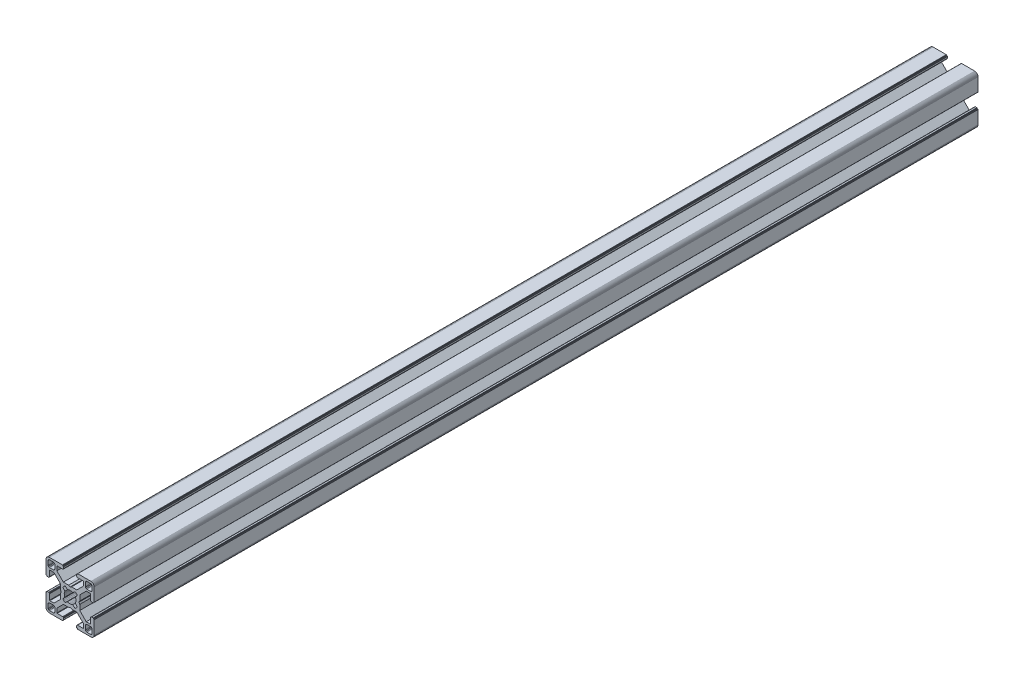
SolidWorks part; units mm, degrees
ref_plane "Front Plane" through (0, 0, 0) normal (0, 0, 1) x (1, 0, 0)
ref_plane "Top Plane" through (0, 0, 0) normal (0, 1, 0) x (1, 0, 0)
ref_plane "Right Plane" through (0, 0, 0) normal (1, 0, 0) x (0, 0, -1)
ref_plane "Plane1" through (0, 0, 0) normal (0, 0, 1) x (1, 0, 0)
sketch "Sketch1" plane through (0, 0, 0) normal (0, 0, 1) x (1, 0, 0)
  line L0 (28.3473, 29.9696) -> (28, 30)
  line L1 (28, 30) -> (19.75, 30)
  line L2 (19.75, 30) -> (19.7153, 29.997)
  line L3 (19.7153, 29.997) -> (19.6816, 29.9879)
  line L4 (19.6816, 29.9879) -> (19.65, 29.9732)
  line L5 (19.65, 29.9732) -> (19.6214, 29.9532)
  line L6 (19.6214, 29.9532) -> (19.5968, 29.9286)
  line L7 (19.5968, 29.9286) -> (19.5768, 29.9)
  line L8 (19.5768, 29.9) -> (19.5621, 29.8684)
  line L9 (19.5621, 29.8684) -> (19.553, 29.8347)
  line L10 (19.553, 29.8347) -> (19.55, 29.8)
  line L11 (19.55, 29.8) -> (19.55, 29.7)
  line L12 (19.55, 29.7) -> (19.547, 29.6653)
  line L13 (19.547, 29.6653) -> (19.5379, 29.6316)
  line L14 (19.5379, 29.6316) -> (19.5232, 29.6)
  line L15 (19.5232, 29.6) -> (19.5032, 29.5714)
  line L16 (19.5032, 29.5714) -> (19.4786, 29.5468)
  line L17 (19.4786, 29.5468) -> (19.45, 29.5268)
  line L18 (19.45, 29.5268) -> (19.4184, 29.5121)
  line L19 (19.4184, 29.5121) -> (19.3847, 29.503)
  line L20 (19.3847, 29.503) -> (19.35, 29.5)
  line L21 (19.35, 29.5) -> (19.25, 29.5)
  line L22 (19.25, 29.5) -> (19.2153, 29.497)
  line L23 (19.2153, 29.497) -> (19.1816, 29.4879)
  line L24 (19.1816, 29.4879) -> (19.15, 29.4732)
  line L25 (19.15, 29.4732) -> (19.1214, 29.4532)
  line L26 (19.1214, 29.4532) -> (19.0968, 29.4286)
  line L27 (19.0968, 29.4286) -> (19.0768, 29.4)
  line L28 (19.0768, 29.4) -> (19.0621, 29.3684)
  line L29 (19.0621, 29.3684) -> (19.053, 29.3347)
  line L30 (19.053, 29.3347) -> (19.05, 29.3)
  line L31 (19.05, 29.3) -> (19.05, 28.4)
  line L32 (19.05, 28.4) -> (19.0591, 28.2958)
  line L33 (19.0591, 28.2958) -> (19.0862, 28.1948)
  line L34 (19.0862, 28.1948) -> (19.1304, 28.1)
  line L35 (19.1304, 28.1) -> (19.1904, 28.0143)
  line L36 (19.1904, 28.0143) -> (19.2643, 27.9404)
  line L37 (19.2643, 27.9404) -> (19.35, 27.8804)
  line L38 (19.35, 27.8804) -> (19.4448, 27.8362)
  line L39 (19.4448, 27.8362) -> (19.5458, 27.8091)
  line L40 (19.5458, 27.8091) -> (19.65, 27.8)
  line L41 (19.65, 27.8) -> (23.05, 27.8)
  line L42 (23.05, 27.8) -> (23.0847, 27.7969)
  line L43 (23.0847, 27.7969) -> (23.1184, 27.7879)
  line L44 (23.1184, 27.7879) -> (23.15, 27.7732)
  line L45 (23.15, 27.7732) -> (23.1786, 27.7532)
  line L46 (23.1786, 27.7532) -> (23.2032, 27.7285)
  line L47 (23.2032, 27.7285) -> (23.2232, 27.7)
  line L48 (23.2232, 27.7) -> (23.2379, 27.6684)
  line L49 (23.2379, 27.6684) -> (23.247, 27.6347)
  line L50 (23.247, 27.6347) -> (23.25, 27.6)
  line L51 (23.25, 27.6) -> (23.25, 25.05)
  line L52 (23.25, 25.05) -> (19.2045, 21)
  line L53 (19.2045, 21) -> (15.9, 21)
  line L54 (15.9, 21) -> (15, 20.4848)
  line L55 (15, 20.4848) -> (14.1, 21)
  line L56 (14.1, 21) -> (10.7955, 21)
  line L57 (10.7955, 21) -> (7.9973, 23.8013)
  line L58 (7.9973, 23.8013) -> (6.75, 25.05)
  line L59 (6.75, 25.05) -> (6.75, 27.6)
  line L60 (6.75, 27.6) -> (6.753, 27.6347)
  line L61 (6.753, 27.6347) -> (6.7621, 27.6684)
  line L62 (6.7621, 27.6684) -> (6.7768, 27.7)
  line L63 (6.7768, 27.7) -> (6.7968, 27.7285)
  line L64 (6.7968, 27.7285) -> (6.8215, 27.7532)
  line L65 (6.8215, 27.7532) -> (6.85, 27.7732)
  line L66 (6.85, 27.7732) -> (6.8816, 27.7879)
  line L67 (6.8816, 27.7879) -> (6.9153, 27.7969)
  line L68 (6.9153, 27.7969) -> (6.95, 27.8)
  line L69 (6.95, 27.8) -> (10.35, 27.8)
  line L70 (10.35, 27.8) -> (10.4542, 27.8091)
  line L71 (10.4542, 27.8091) -> (10.5552, 27.8362)
  line L72 (10.5552, 27.8362) -> (10.65, 27.8804)
  line L73 (10.65, 27.8804) -> (10.7357, 27.9404)
  line L74 (10.7357, 27.9404) -> (10.8096, 28.0143)
  line L75 (10.8096, 28.0143) -> (10.8696, 28.1)
  line L76 (10.8696, 28.1) -> (10.9138, 28.1948)
  line L77 (10.9138, 28.1948) -> (10.9409, 28.2958)
  line L78 (10.9409, 28.2958) -> (10.95, 28.4)
  line L79 (10.95, 28.4) -> (10.95, 29.3)
  line L80 (10.95, 29.3) -> (10.947, 29.3347)
  line L81 (10.947, 29.3347) -> (10.938, 29.3684)
  line L82 (10.938, 29.3684) -> (10.9232, 29.4)
  line L83 (10.9232, 29.4) -> (10.9032, 29.4286)
  line L84 (10.9032, 29.4286) -> (10.8786, 29.4532)
  line L85 (10.8786, 29.4532) -> (10.85, 29.4732)
  line L86 (10.85, 29.4732) -> (10.8184, 29.4879)
  line L87 (10.8184, 29.4879) -> (10.7847, 29.497)
  line L88 (10.7847, 29.497) -> (10.75, 29.5)
  line L89 (10.75, 29.5) -> (10.65, 29.5)
  line L90 (10.65, 29.5) -> (10.6153, 29.503)
  line L91 (10.6153, 29.503) -> (10.5816, 29.5121)
  line L92 (10.5816, 29.5121) -> (10.55, 29.5268)
  line L93 (10.55, 29.5268) -> (10.5214, 29.5468)
  line L94 (10.5214, 29.5468) -> (10.4968, 29.5714)
  line L95 (10.4968, 29.5714) -> (10.4768, 29.6)
  line L96 (10.4768, 29.6) -> (10.4621, 29.6316)
  line L97 (10.4621, 29.6316) -> (10.453, 29.6653)
  line L98 (10.453, 29.6653) -> (10.45, 29.7)
  line L99 (10.45, 29.7) -> (10.45, 29.8)
  line L100 (10.45, 29.8) -> (10.447, 29.8347)
  line L101 (10.447, 29.8347) -> (10.4379, 29.8684)
  line L102 (10.4379, 29.8684) -> (10.4232, 29.9)
  line L103 (10.4232, 29.9) -> (10.4032, 29.9286)
  line L104 (10.4032, 29.9286) -> (10.3786, 29.9532)
  line L105 (10.3786, 29.9532) -> (10.35, 29.9732)
  line L106 (10.35, 29.9732) -> (10.3184, 29.9879)
  line L107 (10.3184, 29.9879) -> (10.2847, 29.997)
  line L108 (10.2847, 29.997) -> (10.25, 30)
  line L109 (10.25, 30) -> (2, 30)
  line L110 (2, 30) -> (1.6527, 29.9696)
  line L111 (1.6527, 29.9696) -> (1.316, 29.8794)
  line L112 (1.316, 29.8794) -> (1, 29.7321)
  line L113 (1, 29.7321) -> (0.7144, 29.5321)
  line L114 (0.7144, 29.5321) -> (0.4679, 29.2856)
  line L115 (0.4679, 29.2856) -> (0.2679, 29)
  line L116 (0.2679, 29) -> (0.1206, 28.684)
  line L117 (0.1206, 28.684) -> (0.0304, 28.3473)
  line L118 (0.0304, 28.3473) -> (0, 28)
  line L119 (0, 28) -> (0, 19.75)
  line L120 (0, 19.75) -> (0.003, 19.7153)
  line L121 (0.003, 19.7153) -> (0.0121, 19.6816)
  line L122 (0.0121, 19.6816) -> (0.0268, 19.65)
  line L123 (0.0268, 19.65) -> (0.0468, 19.6214)
  line L124 (0.0468, 19.6214) -> (0.0714, 19.5968)
  line L125 (0.0714, 19.5968) -> (0.1, 19.5768)
  line L126 (0.1, 19.5768) -> (0.1316, 19.5621)
  line L127 (0.1316, 19.5621) -> (0.1653, 19.553)
  line L128 (0.1653, 19.553) -> (0.2, 19.55)
  line L129 (0.2, 19.55) -> (0.3, 19.55)
  line L130 (0.3, 19.55) -> (0.3347, 19.547)
  line L131 (0.3347, 19.547) -> (0.3684, 19.5379)
  line L132 (0.3684, 19.5379) -> (0.4, 19.5232)
  line L133 (0.4, 19.5232) -> (0.4286, 19.5032)
  line L134 (0.4286, 19.5032) -> (0.4532, 19.4786)
  line L135 (0.4532, 19.4786) -> (0.4732, 19.45)
  line L136 (0.4732, 19.45) -> (0.4879, 19.4184)
  line L137 (0.4879, 19.4184) -> (0.497, 19.3847)
  line L138 (0.497, 19.3847) -> (0.5, 19.35)
  line L139 (0.5, 19.35) -> (0.5, 19.25)
  line L140 (0.5, 19.25) -> (0.503, 19.2153)
  line L141 (0.503, 19.2153) -> (0.5121, 19.1816)
  line L142 (0.5121, 19.1816) -> (0.5268, 19.15)
  line L143 (0.5268, 19.15) -> (0.5468, 19.1214)
  line L144 (0.5468, 19.1214) -> (0.5714, 19.0968)
  line L145 (0.5714, 19.0968) -> (0.6, 19.0768)
  line L146 (0.6, 19.0768) -> (0.6316, 19.0621)
  line L147 (0.6316, 19.0621) -> (0.6653, 19.053)
  line L148 (0.6653, 19.053) -> (0.7, 19.05)
  line L149 (0.7, 19.05) -> (1.6, 19.05)
  line L150 (1.6, 19.05) -> (1.7042, 19.0591)
  line L151 (1.7042, 19.0591) -> (1.8052, 19.0862)
  line L152 (1.8052, 19.0862) -> (1.9, 19.1304)
  line L153 (1.9, 19.1304) -> (1.9857, 19.1904)
  line L154 (1.9857, 19.1904) -> (2.0596, 19.2643)
  line L155 (2.0596, 19.2643) -> (2.1196, 19.35)
  line L156 (2.1196, 19.35) -> (2.1638, 19.4448)
  line L157 (2.1638, 19.4448) -> (2.1909, 19.5458)
  line L158 (2.1909, 19.5458) -> (2.2, 19.65)
  line L159 (2.2, 19.65) -> (2.2, 23.05)
  line L160 (2.2, 23.05) -> (2.203, 23.0847)
  line L161 (2.203, 23.0847) -> (2.2121, 23.1184)
  line L162 (2.2121, 23.1184) -> (2.2268, 23.15)
  line L163 (2.2268, 23.15) -> (2.2468, 23.1786)
  line L164 (2.2468, 23.1786) -> (2.2714, 23.2032)
  line L165 (2.2714, 23.2032) -> (2.3, 23.2232)
  line L166 (2.3, 23.2232) -> (2.3316, 23.2379)
  line L167 (2.3316, 23.2379) -> (2.3653, 23.247)
  line L168 (2.3653, 23.247) -> (2.4, 23.25)
  line L169 (2.4, 23.25) -> (4.95, 23.25)
  line L170 (4.95, 23.25) -> (7.9973, 20.2027)
  line L171 (7.9973, 20.2027) -> (8.9955, 19.2045)
  line L172 (8.9955, 19.2045) -> (8.9955, 15.9)
  line L173 (8.9955, 15.9) -> (9.5151, 15)
  line L174 (9.5151, 15) -> (8.9955, 14.1)
  line L175 (8.9955, 14.1) -> (8.9955, 10.7955)
  line L176 (8.9955, 10.7955) -> (4.95, 6.75)
  line L177 (4.95, 6.75) -> (2.4, 6.75)
  line L178 (2.4, 6.75) -> (2.3653, 6.753)
  line L179 (2.3653, 6.753) -> (2.3316, 6.7621)
  line L180 (2.3316, 6.7621) -> (2.3, 6.7768)
  line L181 (2.3, 6.7768) -> (2.2714, 6.7968)
  line L182 (2.2714, 6.7968) -> (2.2468, 6.8214)
  line L183 (2.2468, 6.8214) -> (2.2268, 6.85)
  line L184 (2.2268, 6.85) -> (2.2121, 6.8816)
  line L185 (2.2121, 6.8816) -> (2.203, 6.9153)
  line L186 (2.203, 6.9153) -> (2.2, 6.95)
  line L187 (2.2, 6.95) -> (2.2, 10.35)
  line L188 (2.2, 10.35) -> (2.1909, 10.4542)
  line L189 (2.1909, 10.4542) -> (2.1638, 10.5552)
  line L190 (2.1638, 10.5552) -> (2.1196, 10.65)
  line L191 (2.1196, 10.65) -> (2.0596, 10.7357)
  line L192 (2.0596, 10.7357) -> (1.9857, 10.8096)
  line L193 (1.9857, 10.8096) -> (1.9, 10.8696)
  line L194 (1.9, 10.8696) -> (1.8052, 10.9138)
  line L195 (1.8052, 10.9138) -> (1.7042, 10.9409)
  line L196 (1.7042, 10.9409) -> (1.6, 10.95)
  line L197 (1.6, 10.95) -> (0.7, 10.95)
  line L198 (0.7, 10.95) -> (0.6653, 10.9469)
  line L199 (0.6653, 10.9469) -> (0.6316, 10.9379)
  line L200 (0.6316, 10.9379) -> (0.6, 10.9232)
  line L201 (0.6, 10.9232) -> (0.5715, 10.9032)
  line L202 (0.5715, 10.9032) -> (0.5468, 10.8785)
  line L203 (0.5468, 10.8785) -> (0.5268, 10.85)
  line L204 (0.5268, 10.85) -> (0.5121, 10.8184)
  line L205 (0.5121, 10.8184) -> (0.503, 10.7847)
  line L206 (0.503, 10.7847) -> (0.5, 10.75)
  line L207 (0.5, 10.75) -> (0.5, 10.65)
  line L208 (0.5, 10.65) -> (0.497, 10.6153)
  line L209 (0.497, 10.6153) -> (0.4879, 10.5816)
  line L210 (0.4879, 10.5816) -> (0.4732, 10.55)
  line L211 (0.4732, 10.55) -> (0.4532, 10.5214)
  line L212 (0.4532, 10.5214) -> (0.4286, 10.4968)
  line L213 (0.4286, 10.4968) -> (0.4, 10.4768)
  line L214 (0.4, 10.4768) -> (0.3684, 10.4621)
  line L215 (0.3684, 10.4621) -> (0.3347, 10.453)
  line L216 (0.3347, 10.453) -> (0.3, 10.45)
  line L217 (0.3, 10.45) -> (0.2, 10.45)
  line L218 (0.2, 10.45) -> (0.1653, 10.447)
  line L219 (0.1653, 10.447) -> (0.1316, 10.4379)
  line L220 (0.1316, 10.4379) -> (0.1, 10.4232)
  line L221 (0.1, 10.4232) -> (0.0714, 10.4032)
  line L222 (0.0714, 10.4032) -> (0.0468, 10.3786)
  line L223 (0.0468, 10.3786) -> (0.0268, 10.35)
  line L224 (0.0268, 10.35) -> (0.0121, 10.3184)
  line L225 (0.0121, 10.3184) -> (0.003, 10.2847)
  line L226 (0.003, 10.2847) -> (0, 10.25)
  line L227 (0, 10.25) -> (0, 2)
  line L228 (0, 2) -> (0.0304, 1.6527)
  line L229 (0.0304, 1.6527) -> (0.1206, 1.316)
  line L230 (0.1206, 1.316) -> (0.2679, 1)
  line L231 (0.2679, 1) -> (0.4679, 0.7144)
  line L232 (0.4679, 0.7144) -> (0.7144, 0.4679)
  line L233 (0.7144, 0.4679) -> (1, 0.2679)
  line L234 (1, 0.2679) -> (1.316, 0.1206)
  line L235 (1.316, 0.1206) -> (1.6527, 0.0304)
  line L236 (1.6527, 0.0304) -> (2, 0)
  line L237 (2, 0) -> (10.25, 0)
  line L238 (10.25, 0) -> (10.2847, 0.003)
  line L239 (10.2847, 0.003) -> (10.3184, 0.0121)
  line L240 (10.3184, 0.0121) -> (10.35, 0.0268)
  line L241 (10.35, 0.0268) -> (10.3786, 0.0468)
  line L242 (10.3786, 0.0468) -> (10.4032, 0.0714)
  line L243 (10.4032, 0.0714) -> (10.4232, 0.1)
  line L244 (10.4232, 0.1) -> (10.4379, 0.1316)
  line L245 (10.4379, 0.1316) -> (10.447, 0.1653)
  line L246 (10.447, 0.1653) -> (10.45, 0.2)
  line L247 (10.45, 0.2) -> (10.45, 0.3)
  line L248 (10.45, 0.3) -> (10.453, 0.3347)
  line L249 (10.453, 0.3347) -> (10.4621, 0.3684)
  line L250 (10.4621, 0.3684) -> (10.4768, 0.4)
  line L251 (10.4768, 0.4) -> (10.4968, 0.4286)
  line L252 (10.4968, 0.4286) -> (10.5214, 0.4532)
  line L253 (10.5214, 0.4532) -> (10.55, 0.4732)
  line L254 (10.55, 0.4732) -> (10.5816, 0.4879)
  line L255 (10.5816, 0.4879) -> (10.6153, 0.497)
  line L256 (10.6153, 0.497) -> (10.65, 0.5)
  line L257 (10.65, 0.5) -> (10.75, 0.5)
  line L258 (10.75, 0.5) -> (10.7847, 0.503)
  line L259 (10.7847, 0.503) -> (10.8184, 0.5121)
  line L260 (10.8184, 0.5121) -> (10.85, 0.5268)
  line L261 (10.85, 0.5268) -> (10.8785, 0.5468)
  line L262 (10.8785, 0.5468) -> (10.9032, 0.5715)
  line L263 (10.9032, 0.5715) -> (10.9232, 0.6)
  line L264 (10.9232, 0.6) -> (10.9379, 0.6316)
  line L265 (10.9379, 0.6316) -> (10.9469, 0.6653)
  line L266 (10.9469, 0.6653) -> (10.95, 0.7)
  line L267 (10.95, 0.7) -> (10.95, 1.6)
  line L268 (10.95, 1.6) -> (10.9409, 1.7042)
  line L269 (10.9409, 1.7042) -> (10.9138, 1.8052)
  line L270 (10.9138, 1.8052) -> (10.8696, 1.9)
  line L271 (10.8696, 1.9) -> (10.8096, 1.9857)
  line L272 (10.8096, 1.9857) -> (10.7357, 2.0596)
  line L273 (10.7357, 2.0596) -> (10.65, 2.1196)
  line L274 (10.65, 2.1196) -> (10.5552, 2.1638)
  line L275 (10.5552, 2.1638) -> (10.4542, 2.1909)
  line L276 (10.4542, 2.1909) -> (10.35, 2.2)
  line L277 (10.35, 2.2) -> (6.95, 2.2)
  line L278 (6.95, 2.2) -> (6.9153, 2.203)
  line L279 (6.9153, 2.203) -> (6.8816, 2.212)
  line L280 (6.8816, 2.212) -> (6.85, 2.2268)
  line L281 (6.85, 2.2268) -> (6.8215, 2.2468)
  line L282 (6.8215, 2.2468) -> (6.7968, 2.2714)
  line L283 (6.7968, 2.2714) -> (6.7768, 2.3)
  line L284 (6.7768, 2.3) -> (6.7621, 2.3316)
  line L285 (6.7621, 2.3316) -> (6.753, 2.3653)
  line L286 (6.753, 2.3653) -> (6.75, 2.4)
  line L287 (6.75, 2.4) -> (6.75, 4.95)
  line L288 (6.75, 4.95) -> (9.7875, 7.9908)
  line L289 (9.7875, 7.9908) -> (10.7955, 9)
  line L290 (10.7955, 9) -> (14.1, 9)
  line L291 (14.1, 9) -> (15, 9.5151)
  line L292 (15, 9.5151) -> (15.9, 9)
  line L293 (15.9, 9) -> (19.2045, 9)
  line L294 (19.2045, 9) -> (20.2126, 7.9908)
  line L295 (20.2126, 7.9908) -> (23.25, 4.95)
  line L296 (23.25, 4.95) -> (23.25, 2.4)
  line L297 (23.25, 2.4) -> (23.247, 2.3653)
  line L298 (23.247, 2.3653) -> (23.2379, 2.3316)
  line L299 (23.2379, 2.3316) -> (23.2232, 2.3)
  line L300 (23.2232, 2.3) -> (23.2032, 2.2714)
  line L301 (23.2032, 2.2714) -> (23.1786, 2.2468)
  line L302 (23.1786, 2.2468) -> (23.15, 2.2268)
  line L303 (23.15, 2.2268) -> (23.1184, 2.212)
  line L304 (23.1184, 2.212) -> (23.0847, 2.203)
  line L305 (23.0847, 2.203) -> (23.05, 2.2)
  line L306 (23.05, 2.2) -> (19.65, 2.2)
  line L307 (19.65, 2.2) -> (19.5458, 2.1909)
  line L308 (19.5458, 2.1909) -> (19.4448, 2.1638)
  line L309 (19.4448, 2.1638) -> (19.35, 2.1196)
  line L310 (19.35, 2.1196) -> (19.2643, 2.0596)
  line L311 (19.2643, 2.0596) -> (19.1904, 1.9857)
  line L312 (19.1904, 1.9857) -> (19.1304, 1.9)
  line L313 (19.1304, 1.9) -> (19.0862, 1.8052)
  line L314 (19.0862, 1.8052) -> (19.0591, 1.7042)
  line L315 (19.0591, 1.7042) -> (19.05, 1.6)
  line L316 (19.05, 1.6) -> (19.05, 0.7)
  line L317 (19.05, 0.7) -> (19.053, 0.6653)
  line L318 (19.053, 0.6653) -> (19.0621, 0.6316)
  line L319 (19.0621, 0.6316) -> (19.0768, 0.6)
  line L320 (19.0768, 0.6) -> (19.0968, 0.5714)
  line L321 (19.0968, 0.5714) -> (19.1214, 0.5468)
  line L322 (19.1214, 0.5468) -> (19.15, 0.5268)
  line L323 (19.15, 0.5268) -> (19.1816, 0.5121)
  line L324 (19.1816, 0.5121) -> (19.2153, 0.503)
  line L325 (19.2153, 0.503) -> (19.25, 0.5)
  line L326 (19.25, 0.5) -> (19.35, 0.5)
  line L327 (19.35, 0.5) -> (19.3847, 0.497)
  line L328 (19.3847, 0.497) -> (19.4184, 0.4879)
  line L329 (19.4184, 0.4879) -> (19.45, 0.4732)
  line L330 (19.45, 0.4732) -> (19.4786, 0.4532)
  line L331 (19.4786, 0.4532) -> (19.5032, 0.4286)
  line L332 (19.5032, 0.4286) -> (19.5232, 0.4)
  line L333 (19.5232, 0.4) -> (19.5379, 0.3684)
  line L334 (19.5379, 0.3684) -> (19.547, 0.3347)
  line L335 (19.547, 0.3347) -> (19.55, 0.3)
  line L336 (19.55, 0.3) -> (19.55, 0.2)
  line L337 (19.55, 0.2) -> (19.553, 0.1653)
  line L338 (19.553, 0.1653) -> (19.5621, 0.1316)
  line L339 (19.5621, 0.1316) -> (19.5768, 0.1)
  line L340 (19.5768, 0.1) -> (19.5968, 0.0714)
  line L341 (19.5968, 0.0714) -> (19.6214, 0.0468)
  line L342 (19.6214, 0.0468) -> (19.65, 0.0268)
  line L343 (19.65, 0.0268) -> (19.6816, 0.0121)
  line L344 (19.6816, 0.0121) -> (19.7153, 0.003)
  line L345 (19.7153, 0.003) -> (19.75, 0)
  line L346 (19.75, 0) -> (28, 0)
  line L347 (28, 0) -> (28.3473, 0.0304)
  line L348 (28.3473, 0.0304) -> (28.684, 0.1206)
  line L349 (28.684, 0.1206) -> (29, 0.2679)
  line L350 (29, 0.2679) -> (29.2856, 0.4679)
  line L351 (29.2856, 0.4679) -> (29.5321, 0.7144)
  line L352 (29.5321, 0.7144) -> (29.7321, 1)
  line L353 (29.7321, 1) -> (29.8794, 1.316)
  line L354 (29.8794, 1.316) -> (29.9696, 1.6527)
  line L355 (29.9696, 1.6527) -> (30, 2)
  line L356 (30, 2) -> (30, 10.25)
  line L357 (30, 10.25) -> (29.997, 10.2847)
  line L358 (29.997, 10.2847) -> (29.988, 10.3184)
  line L359 (29.988, 10.3184) -> (29.9732, 10.35)
  line L360 (29.9732, 10.35) -> (29.9532, 10.3785)
  line L361 (29.9532, 10.3785) -> (29.9286, 10.4032)
  line L362 (29.9286, 10.4032) -> (29.9, 10.4232)
  line L363 (29.9, 10.4232) -> (29.8684, 10.4379)
  line L364 (29.8684, 10.4379) -> (29.8347, 10.447)
  line L365 (29.8347, 10.447) -> (29.8, 10.45)
  line L366 (29.8, 10.45) -> (29.7, 10.45)
  line L367 (29.7, 10.45) -> (29.6649, 10.4534)
  line L368 (29.6649, 10.4534) -> (29.6312, 10.4624)
  line L369 (29.6312, 10.4624) -> (29.5996, 10.4772)
  line L370 (29.5996, 10.4772) -> (29.5711, 10.4972)
  line L371 (29.5711, 10.4972) -> (29.5464, 10.5218)
  line L372 (29.5464, 10.5218) -> (29.5264, 10.5504)
  line L373 (29.5264, 10.5504) -> (29.5117, 10.582)
  line L374 (29.5117, 10.582) -> (29.5027, 10.6156)
  line L375 (29.5027, 10.6156) -> (29.4996, 10.6504)
  line L376 (29.4996, 10.6504) -> (29.4996, 10.7504)
  line L377 (29.4996, 10.7504) -> (29.497, 10.7847)
  line L378 (29.497, 10.7847) -> (29.4879, 10.8184)
  line L379 (29.4879, 10.8184) -> (29.4732, 10.85)
  line L380 (29.4732, 10.85) -> (29.4532, 10.8785)
  line L381 (29.4532, 10.8785) -> (29.4286, 10.9032)
  line L382 (29.4286, 10.9032) -> (29.4, 10.9232)
  line L383 (29.4, 10.9232) -> (29.3684, 10.9379)
  line L384 (29.3684, 10.9379) -> (29.3347, 10.9469)
  line L385 (29.3347, 10.9469) -> (29.3, 10.95)
  line L386 (29.3, 10.95) -> (28.4, 10.95)
  line L387 (28.4, 10.95) -> (28.2958, 10.9409)
  line L388 (28.2958, 10.9409) -> (28.1948, 10.9138)
  line L389 (28.1948, 10.9138) -> (28.1, 10.8696)
  line L390 (28.1, 10.8696) -> (28.0143, 10.8096)
  line L391 (28.0143, 10.8096) -> (27.9404, 10.7357)
  line L392 (27.9404, 10.7357) -> (27.8804, 10.65)
  line L393 (27.8804, 10.65) -> (27.8362, 10.5552)
  line L394 (27.8362, 10.5552) -> (27.8091, 10.4542)
  line L395 (27.8091, 10.4542) -> (27.8, 10.35)
  line L396 (27.8, 10.35) -> (27.8, 6.95)
  line L397 (27.8, 6.95) -> (27.797, 6.9153)
  line L398 (27.797, 6.9153) -> (27.7879, 6.8816)
  line L399 (27.7879, 6.8816) -> (27.7732, 6.85)
  line L400 (27.7732, 6.85) -> (27.7532, 6.8214)
  line L401 (27.7532, 6.8214) -> (27.7286, 6.7968)
  line L402 (27.7286, 6.7968) -> (27.7, 6.7768)
  line L403 (27.7, 6.7768) -> (27.6684, 6.7621)
  line L404 (27.6684, 6.7621) -> (27.6347, 6.753)
  line L405 (27.6347, 6.753) -> (27.6, 6.75)
  line L406 (27.6, 6.75) -> (25.05, 6.75)
  line L407 (25.05, 6.75) -> (23.8092, 7.9908)
  line L408 (23.8092, 7.9908) -> (21.0045, 10.7955)
  line L409 (21.0045, 10.7955) -> (21.0045, 14.1)
  line L410 (21.0045, 14.1) -> (20.4849, 15)
  line L411 (20.4849, 15) -> (21.0045, 15.9)
  line L412 (21.0045, 15.9) -> (21.0045, 19.2045)
  line L413 (21.0045, 19.2045) -> (25.05, 23.25)
  line L414 (25.05, 23.25) -> (27.6, 23.25)
  line L415 (27.6, 23.25) -> (27.6347, 23.247)
  line L416 (27.6347, 23.247) -> (27.6684, 23.2379)
  line L417 (27.6684, 23.2379) -> (27.7, 23.2232)
  line L418 (27.7, 23.2232) -> (27.7286, 23.2032)
  line L419 (27.7286, 23.2032) -> (27.7532, 23.1786)
  line L420 (27.7532, 23.1786) -> (27.7732, 23.15)
  line L421 (27.7732, 23.15) -> (27.7879, 23.1184)
  line L422 (27.7879, 23.1184) -> (27.797, 23.0847)
  line L423 (27.797, 23.0847) -> (27.8, 23.05)
  line L424 (27.8, 23.05) -> (27.8, 19.65)
  line L425 (27.8, 19.65) -> (27.8091, 19.5458)
  line L426 (27.8091, 19.5458) -> (27.8362, 19.4448)
  line L427 (27.8362, 19.4448) -> (27.8804, 19.35)
  line L428 (27.8804, 19.35) -> (27.9404, 19.2643)
  line L429 (27.9404, 19.2643) -> (28.0143, 19.1904)
  line L430 (28.0143, 19.1904) -> (28.1, 19.1304)
  line L431 (28.1, 19.1304) -> (28.1948, 19.0862)
  line L432 (28.1948, 19.0862) -> (28.2958, 19.0591)
  line L433 (28.2958, 19.0591) -> (28.4, 19.05)
  line L434 (28.4, 19.05) -> (29.3, 19.05)
  line L435 (29.3, 19.05) -> (29.3347, 19.053)
  line L436 (29.3347, 19.053) -> (29.3684, 19.0621)
  line L437 (29.3684, 19.0621) -> (29.4, 19.0768)
  line L438 (29.4, 19.0768) -> (29.4282, 19.0971)
  line L439 (29.4282, 19.0971) -> (29.4528, 19.1218)
  line L440 (29.4528, 19.1218) -> (29.4728, 19.1504)
  line L441 (29.4728, 19.1504) -> (29.4876, 19.182)
  line L442 (29.4876, 19.182) -> (29.4966, 19.2156)
  line L443 (29.4966, 19.2156) -> (29.4996, 19.2504)
  line L444 (29.4996, 19.2504) -> (29.4996, 19.3504)
  line L445 (29.4996, 19.3504) -> (29.5027, 19.3851)
  line L446 (29.5027, 19.3851) -> (29.5117, 19.4188)
  line L447 (29.5117, 19.4188) -> (29.5264, 19.4504)
  line L448 (29.5264, 19.4504) -> (29.5464, 19.4789)
  line L449 (29.5464, 19.4789) -> (29.5711, 19.5036)
  line L450 (29.5711, 19.5036) -> (29.5996, 19.5236)
  line L451 (29.5996, 19.5236) -> (29.6312, 19.5383)
  line L452 (29.6312, 19.5383) -> (29.6649, 19.5473)
  line L453 (29.6649, 19.5473) -> (29.7, 19.55)
  line L454 (29.7, 19.55) -> (29.8, 19.55)
  line L455 (29.8, 19.55) -> (29.8347, 19.553)
  line L456 (29.8347, 19.553) -> (29.8684, 19.5621)
  line L457 (29.8684, 19.5621) -> (29.9, 19.5768)
  line L458 (29.9, 19.5768) -> (29.9286, 19.5968)
  line L459 (29.9286, 19.5968) -> (29.9532, 19.6214)
  line L460 (29.9532, 19.6214) -> (29.9732, 19.65)
  line L461 (29.9732, 19.65) -> (29.9879, 19.6816)
  line L462 (29.9879, 19.6816) -> (29.997, 19.7153)
  line L463 (29.997, 19.7153) -> (30, 19.75)
  line L464 (30, 19.75) -> (30, 28)
  line L465 (30, 28) -> (29.9696, 28.3473)
  line L466 (29.9696, 28.3473) -> (29.8794, 28.684)
  line L467 (29.8794, 28.684) -> (29.7321, 29)
  line L468 (29.7321, 29) -> (29.5321, 29.2856)
  line L469 (29.5321, 29.2856) -> (29.2856, 29.5321)
  line L470 (29.2856, 29.5321) -> (29, 29.7321)
  line L471 (29, 29.7321) -> (28.684, 29.8794)
  line L472 (28.684, 29.8794) -> (28.3473, 29.9696)
  line L473 (1.3, 25.5) -> (1.3, 27.7)
  line L474 (1.3, 27.7) -> (1.3123, 27.8564)
  line L475 (1.3123, 27.8564) -> (1.3489, 28.009)
  line L476 (1.3489, 28.009) -> (1.409, 28.154)
  line L477 (1.409, 28.154) -> (1.491, 28.2878)
  line L478 (1.491, 28.2878) -> (1.5929, 28.4071)
  line L479 (1.5929, 28.4071) -> (1.7122, 28.509)
  line L480 (1.7122, 28.509) -> (1.846, 28.591)
  line L481 (1.846, 28.591) -> (1.991, 28.6511)
  line L482 (1.991, 28.6511) -> (2.1436, 28.6877)
  line L483 (2.1436, 28.6877) -> (2.3, 28.7)
  line L484 (2.3, 28.7) -> (4.5, 28.7)
  line L485 (4.5, 28.7) -> (4.6564, 28.6877)
  line L486 (4.6564, 28.6877) -> (4.809, 28.6511)
  line L487 (4.809, 28.6511) -> (4.954, 28.591)
  line L488 (4.954, 28.591) -> (5.0878, 28.509)
  line L489 (5.0878, 28.509) -> (5.2071, 28.4071)
  line L490 (5.2071, 28.4071) -> (5.309, 28.2878)
  line L491 (5.309, 28.2878) -> (5.391, 28.154)
  line L492 (5.391, 28.154) -> (5.4511, 28.009)
  line L493 (5.4511, 28.009) -> (5.4877, 27.8564)
  line L494 (5.4877, 27.8564) -> (5.5, 27.7)
  line L495 (5.5, 27.7) -> (5.5, 25.5)
  line L496 (5.5, 25.5) -> (5.4877, 25.3436)
  line L497 (5.4877, 25.3436) -> (5.4511, 25.191)
  line L498 (5.4511, 25.191) -> (5.391, 25.046)
  line L499 (5.391, 25.046) -> (5.309, 24.9122)
  line L500 (5.309, 24.9122) -> (5.2071, 24.7929)
  line L501 (5.2071, 24.7929) -> (5.0878, 24.691)
  line L502 (5.0878, 24.691) -> (4.954, 24.609)
  line L503 (4.954, 24.609) -> (4.809, 24.5489)
  line L504 (4.809, 24.5489) -> (4.6564, 24.5123)
  line L505 (4.6564, 24.5123) -> (4.5, 24.5)
  line L506 (4.5, 24.5) -> (2.3, 24.5)
  line L507 (2.3, 24.5) -> (2.1436, 24.5123)
  line L508 (2.1436, 24.5123) -> (1.991, 24.5489)
  line L509 (1.991, 24.5489) -> (1.846, 24.609)
  line L510 (1.846, 24.609) -> (1.7122, 24.691)
  line L511 (1.7122, 24.691) -> (1.5929, 24.7929)
  line L512 (1.5929, 24.7929) -> (1.491, 24.9122)
  line L513 (1.491, 24.9122) -> (1.409, 25.046)
  line L514 (1.409, 25.046) -> (1.3489, 25.191)
  line L515 (1.3489, 25.191) -> (1.3123, 25.3436)
  line L516 (1.3123, 25.3436) -> (1.3, 25.5)
  line L517 (25.3436, 28.6877) -> (25.5, 28.7)
  line L518 (25.5, 28.7) -> (27.7, 28.7)
  line L519 (27.7, 28.7) -> (27.8564, 28.6877)
  line L520 (27.8564, 28.6877) -> (28.009, 28.6511)
  line L521 (28.009, 28.6511) -> (28.154, 28.591)
  line L522 (28.154, 28.591) -> (28.2878, 28.509)
  line L523 (28.2878, 28.509) -> (28.4071, 28.4071)
  line L524 (28.4071, 28.4071) -> (28.509, 28.2878)
  line L525 (28.509, 28.2878) -> (28.591, 28.154)
  line L526 (28.591, 28.154) -> (28.6511, 28.009)
  line L527 (28.6511, 28.009) -> (28.6877, 27.8564)
  line L528 (28.6877, 27.8564) -> (28.7, 27.7)
  line L529 (28.7, 27.7) -> (28.7, 25.5)
  line L530 (28.7, 25.5) -> (28.6877, 25.3436)
  line L531 (28.6877, 25.3436) -> (28.6511, 25.191)
  line L532 (28.6511, 25.191) -> (28.591, 25.046)
  line L533 (28.591, 25.046) -> (28.509, 24.9122)
  line L534 (28.509, 24.9122) -> (28.4071, 24.7929)
  line L535 (28.4071, 24.7929) -> (28.2878, 24.691)
  line L536 (28.2878, 24.691) -> (28.154, 24.609)
  line L537 (28.154, 24.609) -> (28.009, 24.5489)
  line L538 (28.009, 24.5489) -> (27.8564, 24.5123)
  line L539 (27.8564, 24.5123) -> (27.7, 24.5)
  line L540 (27.7, 24.5) -> (25.5, 24.5)
  line L541 (25.5, 24.5) -> (25.3436, 24.5123)
  line L542 (25.3436, 24.5123) -> (25.191, 24.5489)
  line L543 (25.191, 24.5489) -> (25.046, 24.609)
  line L544 (25.046, 24.609) -> (24.9122, 24.691)
  line L545 (24.9122, 24.691) -> (24.7929, 24.7929)
  line L546 (24.7929, 24.7929) -> (24.691, 24.9122)
  line L547 (24.691, 24.9122) -> (24.609, 25.046)
  line L548 (24.609, 25.046) -> (24.5489, 25.191)
  line L549 (24.5489, 25.191) -> (24.5123, 25.3436)
  line L550 (24.5123, 25.3436) -> (24.5, 25.5)
  line L551 (24.5, 25.5) -> (24.5, 27.7)
  line L552 (24.5, 27.7) -> (24.5123, 27.8564)
  line L553 (24.5123, 27.8564) -> (24.5489, 28.009)
  line L554 (24.5489, 28.009) -> (24.609, 28.154)
  line L555 (24.609, 28.154) -> (24.691, 28.2878)
  line L556 (24.691, 28.2878) -> (24.7929, 28.4071)
  line L557 (24.7929, 28.4071) -> (24.9122, 28.509)
  line L558 (24.9122, 28.509) -> (25.046, 28.591)
  line L559 (25.046, 28.591) -> (25.191, 28.6511)
  line L560 (25.191, 28.6511) -> (25.3436, 28.6877)
  line L561 (15, 18.65) -> (15.55, 18.6083)
  line L562 (15.55, 18.6083) -> (16.0875, 18.4842)
  line L563 (16.0875, 18.4842) -> (16.6001, 18.2806)
  line L564 (16.6001, 18.2806) -> (18.1359, 19.5184)
  line L565 (18.1359, 19.5184) -> (18.645, 19.1187)
  line L566 (18.645, 19.1187) -> (19.1036, 18.6621)
  line L567 (19.1036, 18.6621) -> (19.5053, 18.1547)
  line L568 (19.5053, 18.1547) -> (18.2806, 16.6001)
  line L569 (18.2806, 16.6001) -> (18.4842, 16.0875)
  line L570 (18.4842, 16.0875) -> (18.6083, 15.55)
  line L571 (18.6083, 15.55) -> (18.65, 15)
  line L572 (18.65, 15) -> (18.6083, 14.45)
  line L573 (18.6083, 14.45) -> (18.4842, 13.9125)
  line L574 (18.4842, 13.9125) -> (18.2806, 13.3999)
  line L575 (18.2806, 13.3999) -> (19.5053, 11.8453)
  line L576 (19.5053, 11.8453) -> (19.1036, 11.3379)
  line L577 (19.1036, 11.3379) -> (18.645, 10.8813)
  line L578 (18.645, 10.8813) -> (18.1359, 10.4816)
  line L579 (18.1359, 10.4816) -> (16.6001, 11.7194)
  line L580 (16.6001, 11.7194) -> (16.0875, 11.5158)
  line L581 (16.0875, 11.5158) -> (15.55, 11.3917)
  line L582 (15.55, 11.3917) -> (15, 11.35)
  line L583 (15, 11.35) -> (14.45, 11.3917)
  line L584 (14.45, 11.3917) -> (13.9125, 11.5158)
  line L585 (13.9125, 11.5158) -> (13.3999, 11.7194)
  line L586 (13.3999, 11.7194) -> (11.8641, 10.4816)
  line L587 (11.8641, 10.4816) -> (11.355, 10.8813)
  line L588 (11.355, 10.8813) -> (10.8964, 11.3379)
  line L589 (10.8964, 11.3379) -> (10.4947, 11.8453)
  line L590 (10.4947, 11.8453) -> (11.7194, 13.3999)
  line L591 (11.7194, 13.3999) -> (11.5158, 13.9125)
  line L592 (11.5158, 13.9125) -> (11.3917, 14.45)
  line L593 (11.3917, 14.45) -> (11.35, 15)
  line L594 (11.35, 15) -> (11.3917, 15.55)
  line L595 (11.3917, 15.55) -> (11.5158, 16.0875)
  line L596 (11.5158, 16.0875) -> (11.7194, 16.6001)
  line L597 (11.7194, 16.6001) -> (10.4947, 18.1547)
  line L598 (10.4947, 18.1547) -> (10.8964, 18.6621)
  line L599 (10.8964, 18.6621) -> (11.355, 19.1187)
  line L600 (11.355, 19.1187) -> (11.8641, 19.5184)
  line L601 (11.8641, 19.5184) -> (13.3999, 18.2806)
  line L602 (13.3999, 18.2806) -> (13.9125, 18.4842)
  line L603 (13.9125, 18.4842) -> (14.45, 18.6083)
  line L604 (14.45, 18.6083) -> (15, 18.65)
  line L605 (4.5, 1.3) -> (2.3, 1.3)
  line L606 (2.3, 1.3) -> (2.1436, 1.3123)
  line L607 (2.1436, 1.3123) -> (1.991, 1.3489)
  line L608 (1.991, 1.3489) -> (1.846, 1.409)
  line L609 (1.846, 1.409) -> (1.7122, 1.491)
  line L610 (1.7122, 1.491) -> (1.5929, 1.5929)
  line L611 (1.5929, 1.5929) -> (1.491, 1.7122)
  line L612 (1.491, 1.7122) -> (1.409, 1.846)
  line L613 (1.409, 1.846) -> (1.3489, 1.991)
  line L614 (1.3489, 1.991) -> (1.3123, 2.1436)
  line L615 (1.3123, 2.1436) -> (1.3, 2.3)
  line L616 (1.3, 2.3) -> (1.3, 4.5)
  line L617 (1.3, 4.5) -> (1.3123, 4.6564)
  line L618 (1.3123, 4.6564) -> (1.3489, 4.809)
  line L619 (1.3489, 4.809) -> (1.409, 4.954)
  line L620 (1.409, 4.954) -> (1.491, 5.0878)
  line L621 (1.491, 5.0878) -> (1.5929, 5.2071)
  line L622 (1.5929, 5.2071) -> (1.7122, 5.309)
  line L623 (1.7122, 5.309) -> (1.846, 5.391)
  line L624 (1.846, 5.391) -> (1.991, 5.4511)
  line L625 (1.991, 5.4511) -> (2.1436, 5.4877)
  line L626 (2.1436, 5.4877) -> (2.3, 5.5)
  line L627 (2.3, 5.5) -> (4.5, 5.5)
  line L628 (4.5, 5.5) -> (4.6564, 5.4877)
  line L629 (4.6564, 5.4877) -> (4.809, 5.4511)
  line L630 (4.809, 5.4511) -> (4.954, 5.391)
  line L631 (4.954, 5.391) -> (5.0878, 5.309)
  line L632 (5.0878, 5.309) -> (5.2071, 5.2071)
  line L633 (5.2071, 5.2071) -> (5.309, 5.0878)
  line L634 (5.309, 5.0878) -> (5.391, 4.954)
  line L635 (5.391, 4.954) -> (5.4511, 4.809)
  line L636 (5.4511, 4.809) -> (5.4877, 4.6564)
  line L637 (5.4877, 4.6564) -> (5.5, 4.5)
  line L638 (5.5, 4.5) -> (5.5, 2.3)
  line L639 (5.5, 2.3) -> (5.4877, 2.1436)
  line L640 (5.4877, 2.1436) -> (5.4511, 1.991)
  line L641 (5.4511, 1.991) -> (5.391, 1.846)
  line L642 (5.391, 1.846) -> (5.309, 1.7122)
  line L643 (5.309, 1.7122) -> (5.2071, 1.5929)
  line L644 (5.2071, 1.5929) -> (5.0878, 1.491)
  line L645 (5.0878, 1.491) -> (4.954, 1.409)
  line L646 (4.954, 1.409) -> (4.809, 1.3489)
  line L647 (4.809, 1.3489) -> (4.6564, 1.3123)
  line L648 (4.6564, 1.3123) -> (4.5, 1.3)
  line L649 (27.7, 1.3) -> (25.5, 1.3)
  line L650 (25.5, 1.3) -> (25.3436, 1.3123)
  line L651 (25.3436, 1.3123) -> (25.191, 1.3489)
  line L652 (25.191, 1.3489) -> (25.046, 1.409)
  line L653 (25.046, 1.409) -> (24.9122, 1.491)
  line L654 (24.9122, 1.491) -> (24.7929, 1.5929)
  line L655 (24.7929, 1.5929) -> (24.691, 1.7122)
  line L656 (24.691, 1.7122) -> (24.609, 1.846)
  line L657 (24.609, 1.846) -> (24.5489, 1.991)
  line L658 (24.5489, 1.991) -> (24.5123, 2.1436)
  line L659 (24.5123, 2.1436) -> (24.5, 2.3)
  line L660 (24.5, 2.3) -> (24.5, 4.5)
  line L661 (24.5, 4.5) -> (24.5123, 4.6564)
  line L662 (24.5123, 4.6564) -> (24.5489, 4.809)
  line L663 (24.5489, 4.809) -> (24.609, 4.954)
  line L664 (24.609, 4.954) -> (24.691, 5.0878)
  line L665 (24.691, 5.0878) -> (24.7929, 5.2071)
  line L666 (24.7929, 5.2071) -> (24.9122, 5.309)
  line L667 (24.9122, 5.309) -> (25.046, 5.391)
  line L668 (25.046, 5.391) -> (25.191, 5.4511)
  line L669 (25.191, 5.4511) -> (25.3436, 5.4877)
  line L670 (25.3436, 5.4877) -> (25.5, 5.5)
  line L671 (25.5, 5.5) -> (27.7, 5.5)
  line L672 (27.7, 5.5) -> (27.8564, 5.4877)
  line L673 (27.8564, 5.4877) -> (28.009, 5.4511)
  line L674 (28.009, 5.4511) -> (28.154, 5.391)
  line L675 (28.154, 5.391) -> (28.2878, 5.309)
  line L676 (28.2878, 5.309) -> (28.4071, 5.2071)
  line L677 (28.4071, 5.2071) -> (28.509, 5.0878)
  line L678 (28.509, 5.0878) -> (28.591, 4.954)
  line L679 (28.591, 4.954) -> (28.6511, 4.809)
  line L680 (28.6511, 4.809) -> (28.6877, 4.6564)
  line L681 (28.6877, 4.6564) -> (28.7, 4.5)
  line L682 (28.7, 4.5) -> (28.7, 2.3)
  line L683 (28.7, 2.3) -> (28.6877, 2.1436)
  line L684 (28.6877, 2.1436) -> (28.6511, 1.991)
  line L685 (28.6511, 1.991) -> (28.591, 1.846)
  line L686 (28.591, 1.846) -> (28.509, 1.7122)
  line L687 (28.509, 1.7122) -> (28.4071, 1.5929)
  line L688 (28.4071, 1.5929) -> (28.2878, 1.491)
  line L689 (28.2878, 1.491) -> (28.154, 1.409)
  line L690 (28.154, 1.409) -> (28.009, 1.3489)
  line L691 (28.009, 1.3489) -> (27.8564, 1.3123)
  line L692 (27.8564, 1.3123) -> (27.7, 1.3)
extrude "Boss-Extrude1" add sketch "Sketch1" against normal blind 550
